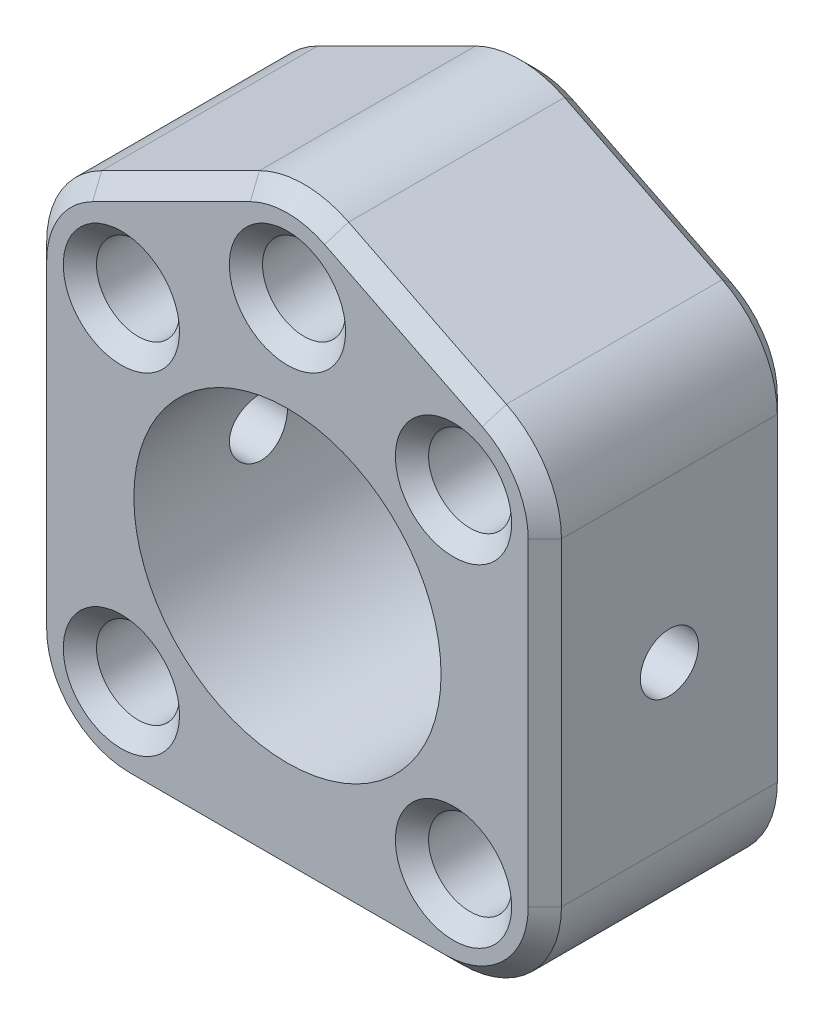
SolidWorks part; units mm, degrees
ref_plane "正面(Front)" through (0, 0, 0) normal (0, 0, 1) x (1, 0, 0)
ref_plane "平面(Top)" through (0, 0, 0) normal (0, 1, 0) x (1, 0, 0)
ref_plane "右側面(Right)" through (0, 0, 0) normal (1, 0, 0) x (0, 0, -1)
sketch "ｽｹｯﾁ1" plane through (0, 0, 0) normal (0, 0, 1) x (1, 0, 0)
  line L0 (0, 0) -> (0, 15) construction
  line L1 (10, 10) -> (-10, 10) construction
  line L2 (10, 10) -> (10, -10) construction
  line L3 (10, -10) -> (-10, -10) construction
  line L4 (-10, 10) -> (-10, -10) construction
  line L5 (10, 10) -> (-10, -10) construction
  line L6 (10, -10) -> (-10, 10) construction
  line L7 (2.6833, 19.8075) -> (12.1833, 15.0575)
  line L8 (15.5, 9.691) -> (15.5, -9.5)
  line L9 (9.5, -15.5) -> (-9.5, -15.5)
  line L10 (0, 15) -> (10, 10) construction
  line L11 (-15.5, 9.691) -> (-15.5, -9.5)
  line L12 (-2.6833, 19.8075) -> (-12.1833, 15.0575)
  circle A0 centre (0, 0) radius 9.25
  circle A1 centre (-10, -10) radius 2.5
  circle A2 centre (-10, 10) radius 2.5
  circle A3 centre (10, 10) radius 2.5
  circle A4 centre (10, -10) radius 2.5
  circle A5 centre (0, 15) radius 2.5
  arc A6 (-15.5, -9.5) -> (-9.5, -15.5) centre (-9.5, -9.5) ccw
  arc A7 (-15.5, 9.691) -> (-12.1833, 15.0575) centre (-9.5, 9.691) cw
  arc A8 (2.6833, 19.8075) -> (-2.6833, 19.8075) centre (0, 14.441) ccw
  arc A9 (12.1833, 15.0575) -> (15.5, 9.691) centre (9.5, 9.691) cw
  arc A10 (15.5, -9.5) -> (9.5, -15.5) centre (9.5, -9.5) cw
  point P19 (0, -15.5)
  point P22 (-15.5, -15.5)
  point P25 (-15.5, 13.3992)
  point P28 (0, 21.1492)
  point P31 (15.5, 13.3992)
  point P34 (15.5, -15.5)
  dimension "D1" = 18.5
  dimension "D4" = 5
  dimension "D5" = 5
  dimension "D7" = 3
  dimension "D8" = 3
  dimension "D9" = 3
  dimension "D10" = 6
  dimension "D2" = 20
  dimension "D3" = 20
  dimension "D6" = 15
extrude "ﾎﾞｽ - 押し出し1" add sketch "ｽｹｯﾁ1" along normal mid plane 15
sketch "ｽｹｯﾁ3" plane through (0, 0, 0) normal (1, 0, 0) x (0, 0, -1)
  circle A0 centre (0, 0) radius 1.75
  dimension "D1" = 3.5
extrude "ｶｯﾄ - 押し出し1" cut sketch "ｽｹｯﾁ3" against normal through all both and the other way through all
chamfer "面取り1" distance 1 angle 45 10 edges at (-7.5, -10, -7.5) (-7.5, 10, -7.5) (2.5, 15, -7.5) (12.5, 10, -7.5) (12.5, -10, -7.5) (-7.5, 10, 7.5) (2.5, 15, 7.5) (12.5, 10, 7.5) (12.5, -10, 7.5) (-7.5, -10, 7.5)
chamfer "面取り2" distance 1 angle 45 20 edges at (14.6039, 12.8454, 7.5) (7.4333, 17.4325, 7.5) (15.5, 0.0955, 7.5) (0, 20.441, 7.5) (13.7426, -13.7426, 7.5) (-7.4333, 17.4325, 7.5) (0, -15.5, 7.5) (-14.6039, 12.8454, 7.5) (-13.7426, -13.7426, 7.5) (-15.5, 0.0955, 7.5) (14.6039, 12.8454, -7.5) (7.4333, 17.4325, -7.5) (15.5, 0.0955, -7.5) (0, 20.441, -7.5) (13.7426, -13.7426, -7.5) (-7.4333, 17.4325, -7.5) (0, -15.5, -7.5) (-14.6039, 12.8454, -7.5) (-13.7426, -13.7426, -7.5) (-15.5, 0.0955, -7.5)
